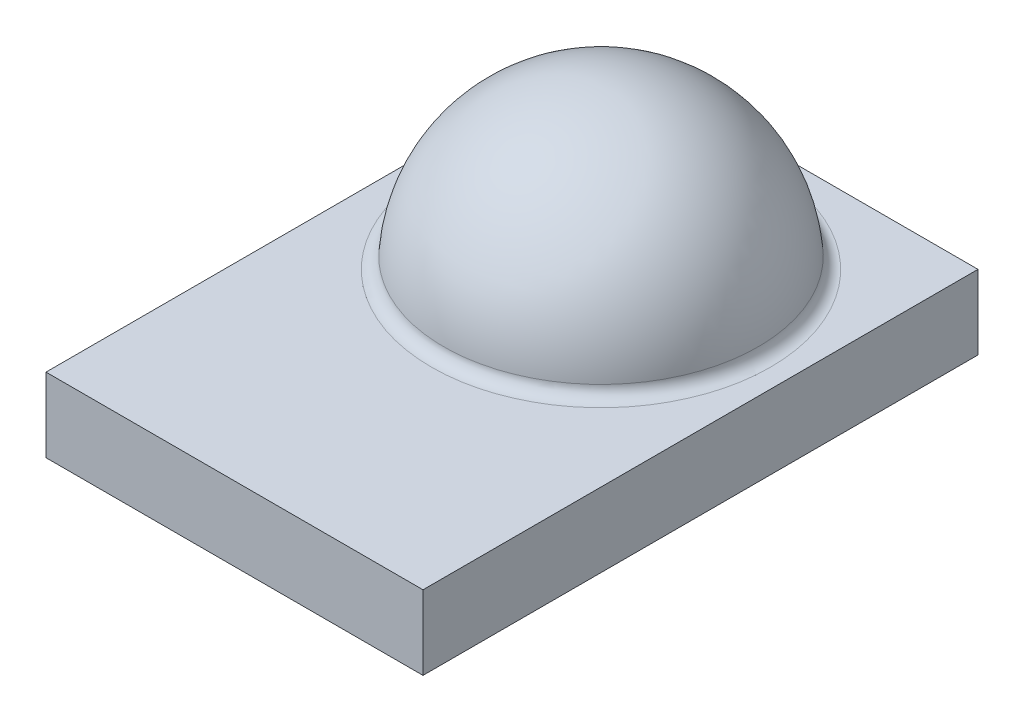
SolidWorks part; units mm, degrees
ref_plane "Front Plane" through (0, 0, 0) normal (0, 0, 1) x (1, 0, 0)
ref_plane "Top Plane" through (0, 0, 0) normal (0, 1, 0) x (1, 0, 0)
ref_plane "Right Plane" through (0, 0, 0) normal (1, 0, 0) x (0, 0, -1)
sketch "Sketch1" plane through (0, 0, 0) normal (0, 1, 0) x (1, 0, 0)
  line L1 (0, 0) -> (3.05, 0)
  line L2 (0, 0) -> (0, 4.49)
  line L3 (0, 4.49) -> (3.05, 4.49)
  line L4 (3.05, 0) -> (3.05, 4.49)
  dimension "D1" = 3.05
  dimension "D2" = 4.49
extrude "Boss-Extrude1" add sketch "Sketch1" along normal blind 0.6
sketch "Sketch2" plane through (0, 0.6, 0) normal (0, 1, 0) x (1, 0, 0)
  line L0 (1.525, 4.49) -> (1.525, 0) construction
  line L1 (3.05, 4.49) -> (0, 4.49) construction
  line L2 (0, 0) -> (3.05, 0) construction
  line L3 (0.25, 2.965) -> (2.8, 2.965)
  arc A0 (2.8, 2.965) -> (0.25, 2.965) centre (1.525, 2.965) ccw
  dimension "D2" = 2.55
  dimension "D1" = 1.525
revolve "Revolve1" add sketch "Sketch2" angle 180 about L3
fillet "Fillet1" radius 0.1 1 edges at (1.525, 0.6, -4.24)
sketch "Sketch3" plane through (0, 0, 0) normal (0, -1, 0) x (1, 0, 0)
  line L1 (0.125, -4.365) -> (2.925, -4.365)
  line L2 (0.125, -4.365) -> (0.125, -2.595)
  line L3 (0.125, -2.595) -> (2.925, -2.595)
  line L4 (2.925, -4.365) -> (2.925, -2.595)
  line L5 (0.125, -0.125) -> (1.325, -0.125)
  line L6 (0.125, -0.125) -> (0.125, -0.795)
  line L7 (0.125, -0.795) -> (1.325, -0.795)
  line L8 (1.325, -0.125) -> (1.325, -0.795)
  line L9 (1.725, -0.125) -> (2.925, -0.125)
  line L10 (1.725, -0.125) -> (1.725, -0.795)
  line L11 (1.725, -0.795) -> (2.925, -0.795)
  line L12 (2.925, -0.125) -> (2.925, -0.795)
  line L13 (0, -4.49) -> (0, 0) construction
  line L16 (3.05, 0) -> (3.05, -4.49) construction
  line L17 (3.05, -4.49) -> (0, -4.49) construction
  point P12 (0.725, -0.795)
  dimension "D1" = 0.67
  dimension "D2" = 1.2
  dimension "D3" = 2.8
  dimension "D4" = 1.77
  dimension "D5" = 1.8
  dimension "D6" = 0.125
  dimension "D7" = 0.125
  dimension "D8" = 0.125
  dimension "D9" = 0.125
extrude "Boss-Extrude2" add sketch "Sketch3" along normal blind 0.08
